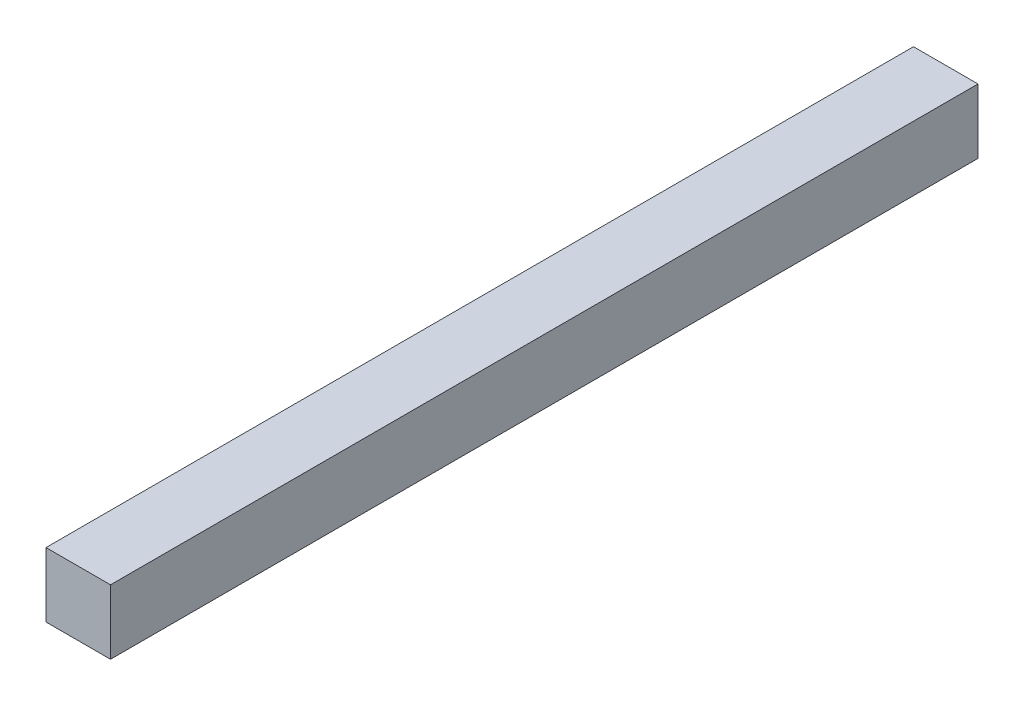
SolidWorks part; units mm, degrees
material "Balsa"
ref_plane "Front Plane" through (0, 0, 0) normal (0, 0, 1) x (1, 0, 0)
ref_plane "Top Plane" through (0, 0, 0) normal (0, 1, 0) x (1, 0, 0)
ref_plane "Right Plane" through (0, 0, 0) normal (1, 0, 0) x (0, 0, -1)
sketch "Sketch1" plane through (0, 0, 0) normal (0, 0, 1) x (1, 0, 0)
  line L1 (0, 0) -> (3.175, 0)
  line L2 (0, 0) -> (0, 3.175)
  line L3 (0, 3.175) -> (3.175, 3.175)
  line L4 (3.175, 0) -> (3.175, 3.175)
  dimension "D1" = 3.175
extrude "Boss-Extrude1" add sketch "Sketch1" along normal blind 42.7
